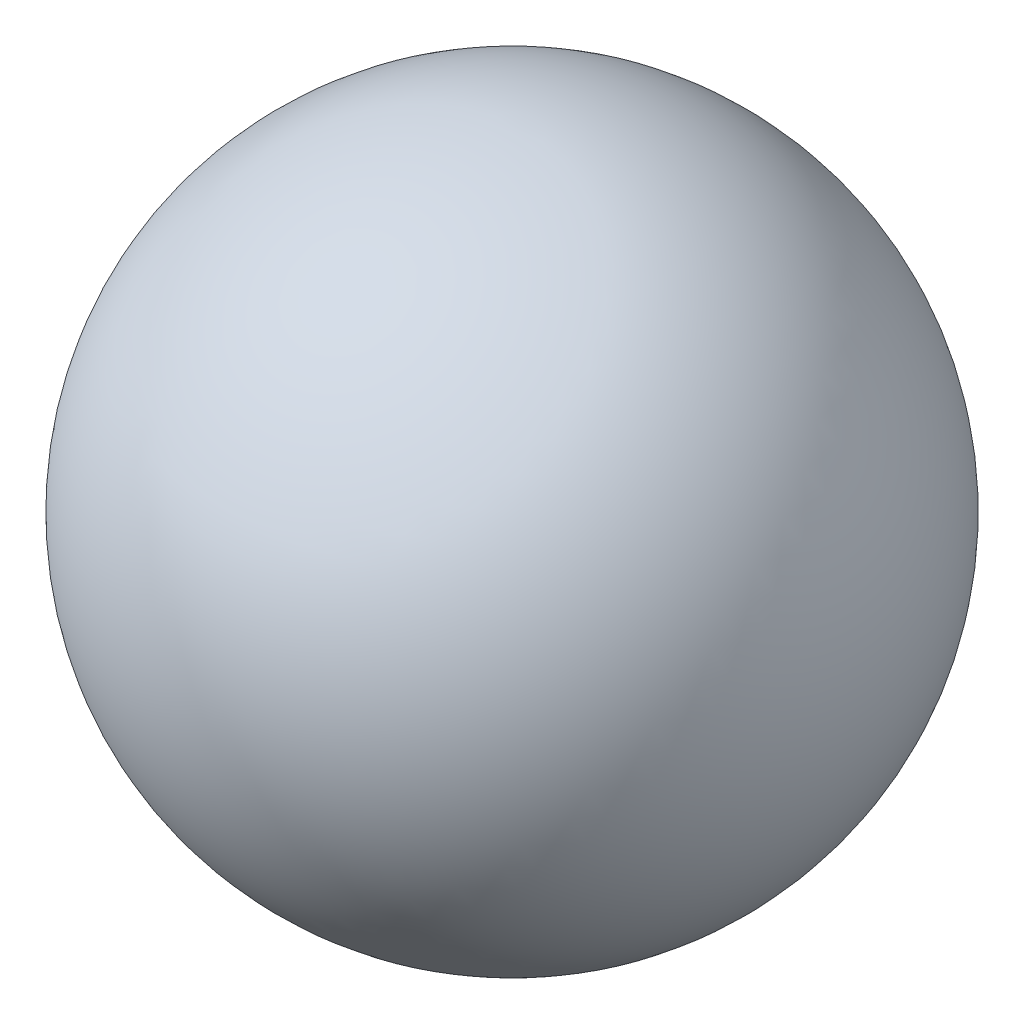
SolidWorks part; units mm, degrees
ref_plane "Front Plane" through (0, 0, 0) normal (0, 0, 1) x (1, 0, 0)
ref_plane "Top Plane" through (0, 0, 0) normal (0, 1, 0) x (1, 0, 0)
ref_plane "Right Plane" through (0, 0, 0) normal (1, 0, 0) x (0, 0, -1)
sketch "Sketch1" plane through (0, 0, 0) normal (0, 0, 1) x (1, 0, 0)
  line L0 (0, 510) -> (0, -510)
  arc A0 (0, -510) -> (0, 510) centre (0, 0) ccw
  dimension "D1" = 1020
revolve "Revolve1" add sketch "Sketch1" angle 360 about L0
